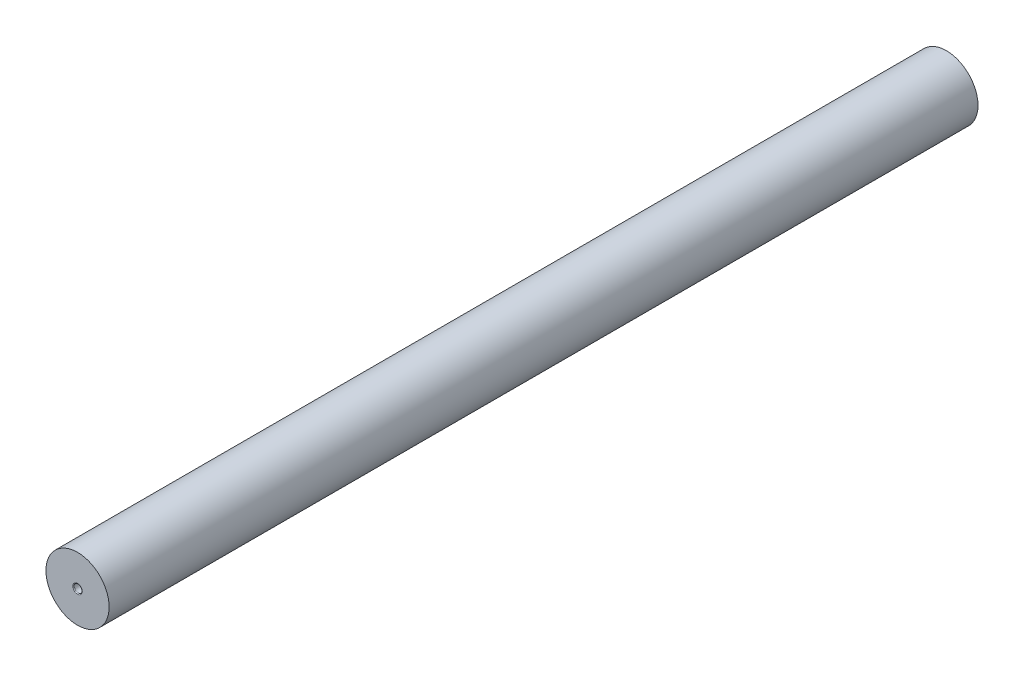
SolidWorks part; units mm, degrees
ref_plane "Ön Düzlem" through (0, 0, 0) normal (0, 0, 1) x (1, 0, 0)
ref_plane "Üst Düzlem" through (0, 0, 0) normal (0, 1, 0) x (1, 0, 0)
ref_plane "Sağ Düzlem" through (0, 0, 0) normal (1, 0, 0) x (0, 0, -1)
sketch "Çizim1" plane through (0, 0, 0) normal (0, 0, 1) x (1, 0, 0)
  circle A0 centre (0, 0) radius 4
  dimension "D1" = 8
extrude "Yükseklik-Ekstrüzyon1" add sketch "Çizim1" along normal blind 110
sketch "Çizim2" plane through (0, 0, 110) normal (0, 0, 1) x (1, 0, 0)
  circle A0 centre (0, 0) radius 0.5
  dimension "D1" = 1
extrude "Kes-Ekstrüzyon1" cut sketch "Çizim2" against normal blind 5
fillet "Radyus1" radius 0.1 1 edges at (0.5, 0, 110)
